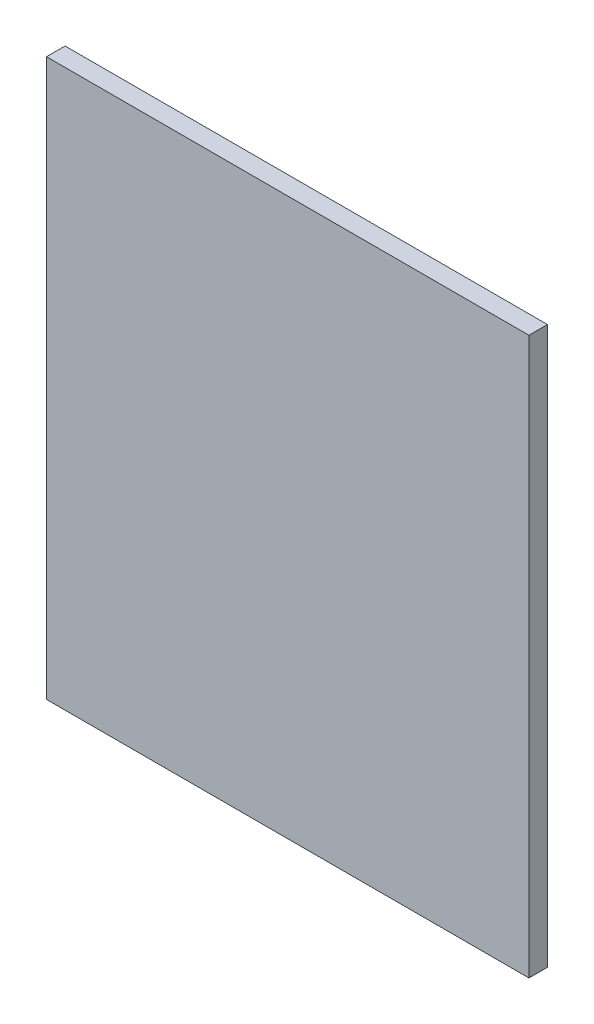
SolidWorks part; units mm, degrees
ref_plane "Plano frontal" through (0, 0, 0) normal (0, 0, 1) x (1, 0, 0)
ref_plane "Plano superior" through (0, 0, 0) normal (0, 1, 0) x (1, 0, 0)
ref_plane "Plano direito" through (0, 0, 0) normal (1, 0, 0) x (0, 0, -1)
sketch "Esboço1" plane through (0, 0, 0) normal (0, 0, 1) x (1, 0, 0)
  line L1 (0, 0) -> (52, 0)
  line L2 (0, 0) -> (0, 60)
  line L3 (0, 60) -> (52, 60)
  line L4 (52, 0) -> (52, 60)
  dimension "D1" = 52
  dimension "D2" = 60
extrude "Ressalto-extrusão1" add sketch "Esboço1" along normal blind 2
